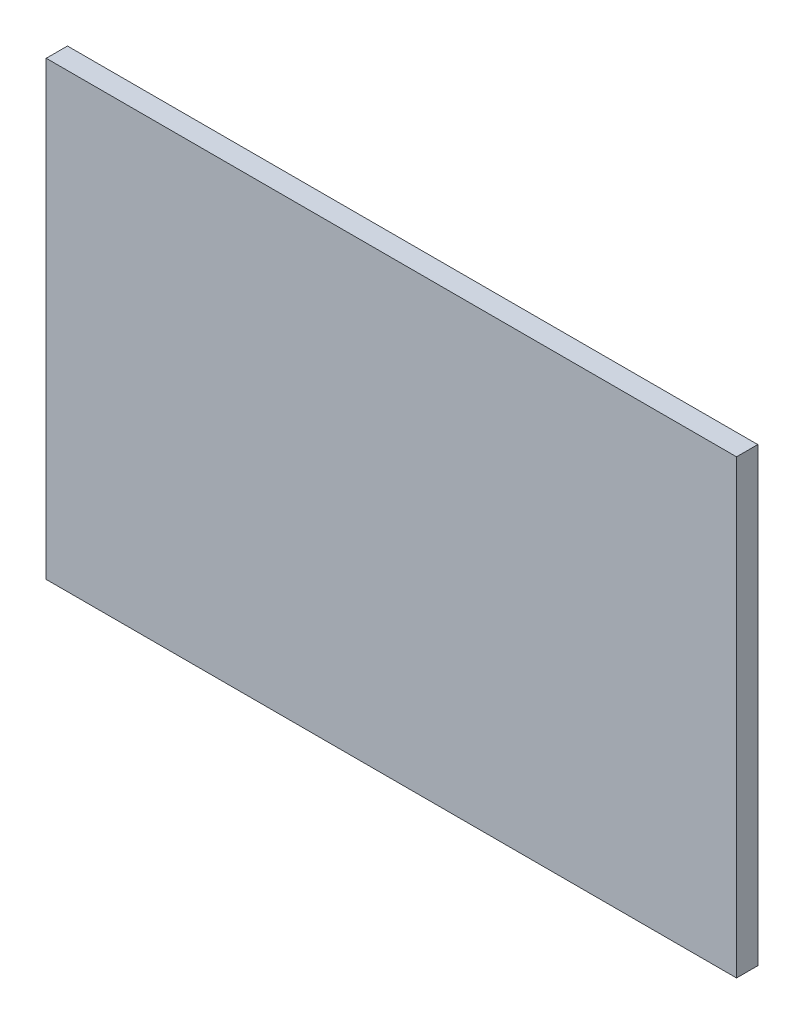
SolidWorks part; units mm, degrees
ref_plane "Front Plane" through (0, 0, 0) normal (0, 0, 1) x (1, 0, 0)
ref_plane "Top Plane" through (0, 0, 0) normal (0, 1, 0) x (1, 0, 0)
ref_plane "Right Plane" through (0, 0, 0) normal (1, 0, 0) x (0, 0, -1)
sketch "Sketch1" plane through (0, 0, 0) normal (0, 0, 1) x (1, 0, 0)
  line L1 (0, 0) -> (26, 0)
  line L2 (0, 0) -> (0, -17)
  line L3 (0, -17) -> (26, -17)
  line L4 (26, 0) -> (26, -17)
  dimension "D1" = 26
  dimension "D2" = 17
extrude "Boss-Extrude1" add sketch "Sketch1" along normal blind 0.8
